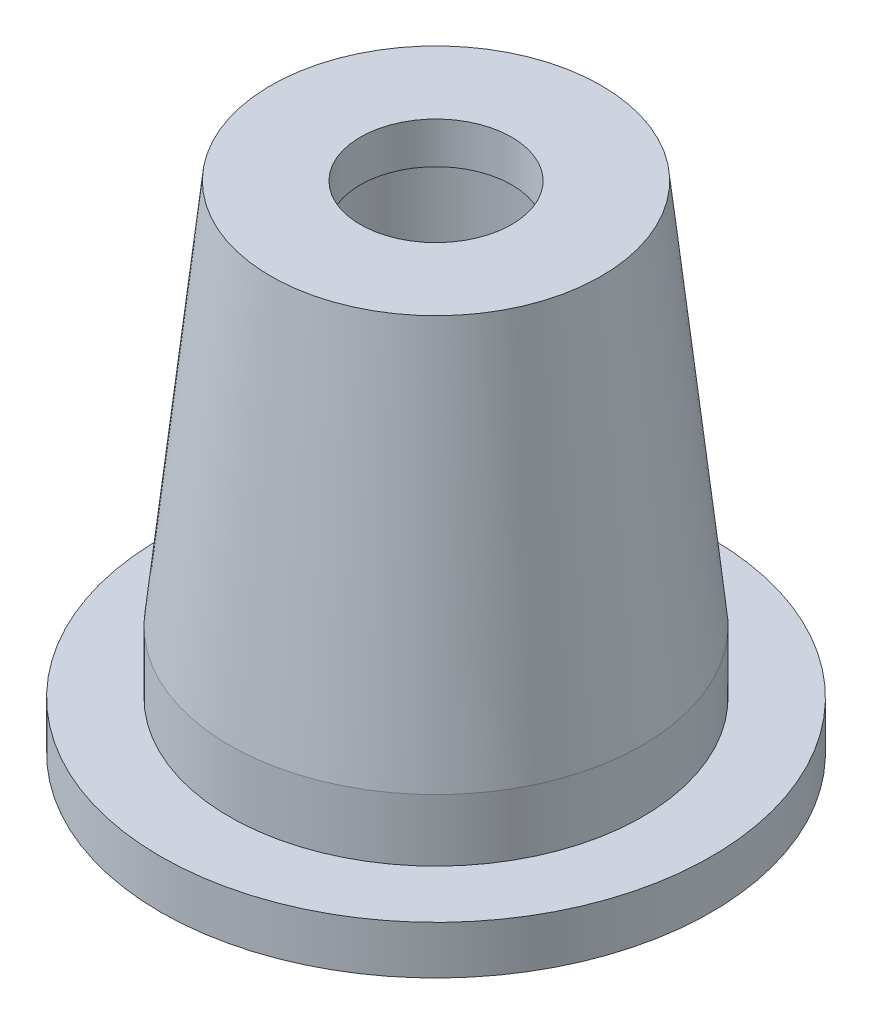
SolidWorks part; units mm, degrees
material "Сталь"
ref_plane "Спереди" through (0, 0, 0) normal (0, 0, 1) x (1, 0, 0)
ref_plane "Сверху" through (0, 0, 0) normal (0, 1, 0) x (1, 0, 0)
ref_plane "Справа" through (0, 0, 0) normal (1, 0, 0) x (0, 0, -1)
sketch "Эскиз1" plane through (0, 0, 0) normal (0, 0, 1) x (1, 0, 0)
  line L0 (9, 0) -> (20, 0)
  line L1 (20, 0) -> (20, 3.5)
  line L2 (20, 3.5) -> (15, 3.5)
  line L3 (15, 3.5) -> (15, 8)
  line L4 (15, 8) -> (12, 36)
  line L5 (12, 36) -> (5.5, 36)
  line L6 (5.5, 36) -> (5.5, 33)
  line L7 (5.5, 33) -> (9, 33)
  line L8 (9, 33) -> (9, 0)
  line L9 (0, 0) -> (0, 30.5779) construction
  dimension "D1" = 20
  dimension "D2" = 3.5
  dimension "D3" = 15
  dimension "D4" = 4.5
  dimension "D5" = 9
  dimension "D6" = 12
  dimension "D7" = 36
  dimension "D8" = 6.5
  dimension "D9" = 33
revolve "Повернуть1" add sketch "Эскиз1" angle 360 about L9
sketch "Эскиз2" plane through (0, 0, 0) normal (0, 0, 1) x (1, 0, 0)
  line L0 (15.5, -3.5) -> (15.5, -0.5) construction
  line L2 (13.5, -3.5) -> (13.5, -0.5)
  line L3 (17.5, -3.5) -> (17.5, -0.5)
  line L4 (0, 0) -> (0, 3.5) construction
  line L5 (20, 3.5) -> (-20, 3.5) construction
  arc A0 (13.5, -3.5) -> (17.5, -3.5) centre (15.5, -3.5) ccw
  arc A1 (17.5, -0.5) -> (13.5, -0.5) centre (15.5, -0.5) ccw
  point P4 (15.5, -2)
  dimension "D2" = 2
  dimension "D1" = 15.5
  dimension "D3" = 3
  dimension "D4" = 2
revolve "Вырез-Повернуть1" cut sketch "Эскиз2" angle 360 about L4
chamfer "Фаска1" distance 3 angle 45 1 edges at (0, 0, -9)
